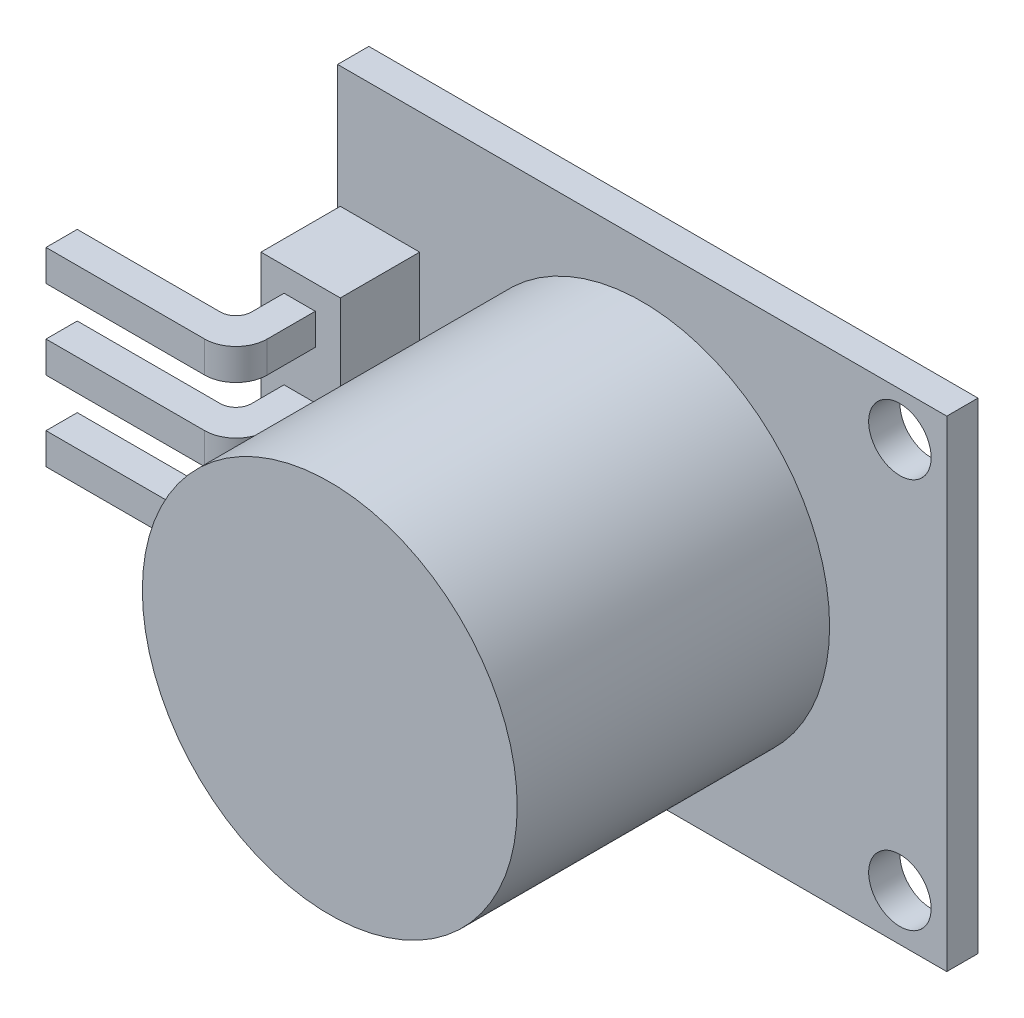
SolidWorks part; units mm, degrees
ref_plane "Alzado" through (0, 0, 0) normal (0, 0, 1) x (1, 0, 0)
ref_plane "Planta" through (0, 0, 0) normal (0, 1, 0) x (1, 0, 0)
ref_plane "Vista lateral" through (0, 0, 0) normal (1, 0, 0) x (0, 0, -1)
sketch "Croquis1" plane through (0, 0, 0) normal (0, 0, 1) x (1, 0, 0)
  line L0 (-9.363, 12.507) -> (-9.363, -2.893) construction
  line L1 (-19.113, 12.507) -> (0.387, 12.507)
  line L2 (-19.113, 12.507) -> (-19.113, -2.893)
  line L3 (-19.113, -2.893) -> (0.387, -2.893)
  line L4 (0.387, 12.507) -> (0.387, -2.893)
  line L5 (-32.967, 10.007) -> (-19.113, 10.007) construction
  line L6 (-32.967, 10.007) -> (-32.967, 0.007)
  line L7 (-32.967, 0.007) -> (-19.113, 0.007)
  line L8 (-19.113, 10.007) -> (-19.113, 0.007)
  circle A0 centre (-9.363, 4.807) radius 6 construction
  circle A1 centre (-1.113, 11.107) radius 1
  circle A2 centre (-1.113, -1.393) radius 1
  dimension "D5" = 12.5
  dimension "D6" = 1.5
  dimension "D7" = 1.5
  dimension "D1" = 19.5
  dimension "D2" = 15.4
  dimension "D3" = 10
  dimension "D4" = 2.9
extrude "Saliente-Extruir1" add sketch "Croquis1" along normal blind 1 contours L4 L1 L2 L3 A2 A1
sketch "Croquis2" plane through (0, 0, 1) normal (0, 0, 1) x (1, 0, 0)
  line L0 (-9.363, 12.507) -> (-9.363, -2.893) construction
  line L1 (-19.113, 12.507) -> (0.387, 12.507) construction
  line L2 (-19.113, -2.893) -> (0.387, -2.893) construction
  circle A0 centre (-9.363, 4.807) radius 6
extrude "Saliente-Extruir2" add sketch "Croquis2" along normal blind 10
sketch "Croquis3" plane through (0, 0, 1) normal (0, 0, 1) x (1, 0, 0)
  line L1 (-16.4857, 8.617) -> (-16.4857, 0.997)
  line L2 (-16.4857, 0.997) -> (-19.0257, 0.997)
  line L3 (-19.0257, 0.997) -> (-19.0257, 8.617)
  line L4 (-19.0257, 8.617) -> (-16.4857, 8.617)
  line L5 (-17.7557, 8.617) -> (-17.7557, 0.997) construction
  line L6 (-19.113, 4.807) -> (0.387, 4.807) construction
  line L7 (-19.113, 12.507) -> (-19.113, -2.893) construction
  line L8 (0.387, 12.507) -> (0.387, -2.893) construction
  dimension "D1" = 2.54
  dimension "D2" = 7.62
extrude "Saliente-Extruir3" add sketch "Croquis3" along normal blind 2.54
sketch "Croquis4" plane through (0, 0, 3.54) normal (0, 0, 1) x (1, 0, 0)
  line L0 (-18.2868, 7.847) -> (-17.2868, 7.847)
  line L1 (-17.2868, 7.847) -> (-17.2868, 6.847)
  line L2 (-17.2868, 6.847) -> (-18.2868, 6.847)
  line L3 (-18.2868, 6.847) -> (-18.2868, 7.847)
  line L4 (-18.2868, 5.307) -> (-17.2868, 5.307)
  line L5 (-17.2868, 5.307) -> (-17.2868, 4.307)
  line L6 (-17.2868, 4.307) -> (-18.2868, 4.307)
  line L7 (-18.2868, 4.307) -> (-18.2868, 5.307)
  line L8 (-18.2868, 2.767) -> (-17.2868, 2.767)
  line L9 (-17.2868, 2.767) -> (-17.2868, 1.767)
  line L10 (-17.2868, 1.767) -> (-18.2868, 1.767)
  line L11 (-18.2868, 1.767) -> (-18.2868, 2.767)
  line L12 (-18.2868, 4.807) -> (-17.2868, 4.807) construction
  line L13 (-18.2868, 7.347) -> (-17.2868, 7.347) construction
  line L14 (-18.2868, 2.267) -> (-17.2868, 2.267) construction
  line L15 (-16.4857, 8.617) -> (-19.0257, 8.617) construction
  dimension "D1" = 2.54
  dimension "D2" = 2.54
  dimension "D3" = 0.77
  dimension "D4" = 1
  dimension "D5" = 1
  dimension "D6" = 1
  dimension "D7" = 1
  dimension "D8" = 1
  dimension "D9" = 1
extrude "Saliente-Extruir4" add sketch "Croquis4" along normal blind 2.54
sketch "Croquis6" plane through (-18.2868, 0, 0) normal (-1, 0, 0) x (0, 0, 1)
  line L0 (6.08, 5.307) -> (6.08, 4.307)
  line L1 (6.08, 4.307) -> (5.08, 4.307)
  line L2 (6.08, 4.307) -> (3.54, 4.307) construction
  line L3 (5.08, 4.307) -> (5.08, 5.307)
  line L4 (6.08, 5.307) -> (3.54, 5.307) construction
  line L5 (5.08, 5.307) -> (6.08, 5.307)
  line L10 (6.08, 2.767) -> (5.08, 2.767)
  line L11 (6.08, 2.767) -> (3.54, 2.767) construction
  line L12 (5.08, 2.767) -> (5.08, 1.767)
  line L13 (6.08, 1.767) -> (3.54, 1.767) construction
  line L14 (5.08, 1.767) -> (6.08, 1.767)
  line L15 (6.08, 1.767) -> (6.08, 2.767)
  line L16 (6.08, 7.847) -> (6.08, 6.847)
  line L17 (6.08, 6.847) -> (5.08, 6.847)
  line L18 (6.08, 6.847) -> (3.54, 6.847) construction
  line L19 (5.08, 6.847) -> (5.08, 7.847)
  line L20 (6.08, 7.847) -> (3.54, 7.847) construction
  line L21 (5.08, 7.847) -> (6.08, 7.847)
  dimension "D1" = 1
  dimension "D2" = 1
  dimension "D3" = 1
extrude "Saliente-Extruir5" add sketch "Croquis6" along normal blind 5.08
fillet "Redondeo2" radius 1 1 edges at (-17.2868, 2.267, 6.08)
fillet "Redondeo3" radius 1 1 edges at (-17.2868, 4.807, 6.08)
fillet "Redondeo4" radius 1 1 edges at (-17.2868, 7.347, 6.08)
fillet "Redondeo5" radius 0.5 1 edges at (-18.2868, 2.267, 5.08)
fillet "Redondeo6" radius 0.5 1 edges at (-18.2868, 4.807, 5.08)
fillet "Redondeo7" radius 0.5 1 edges at (-18.2868, 7.347, 5.08)
